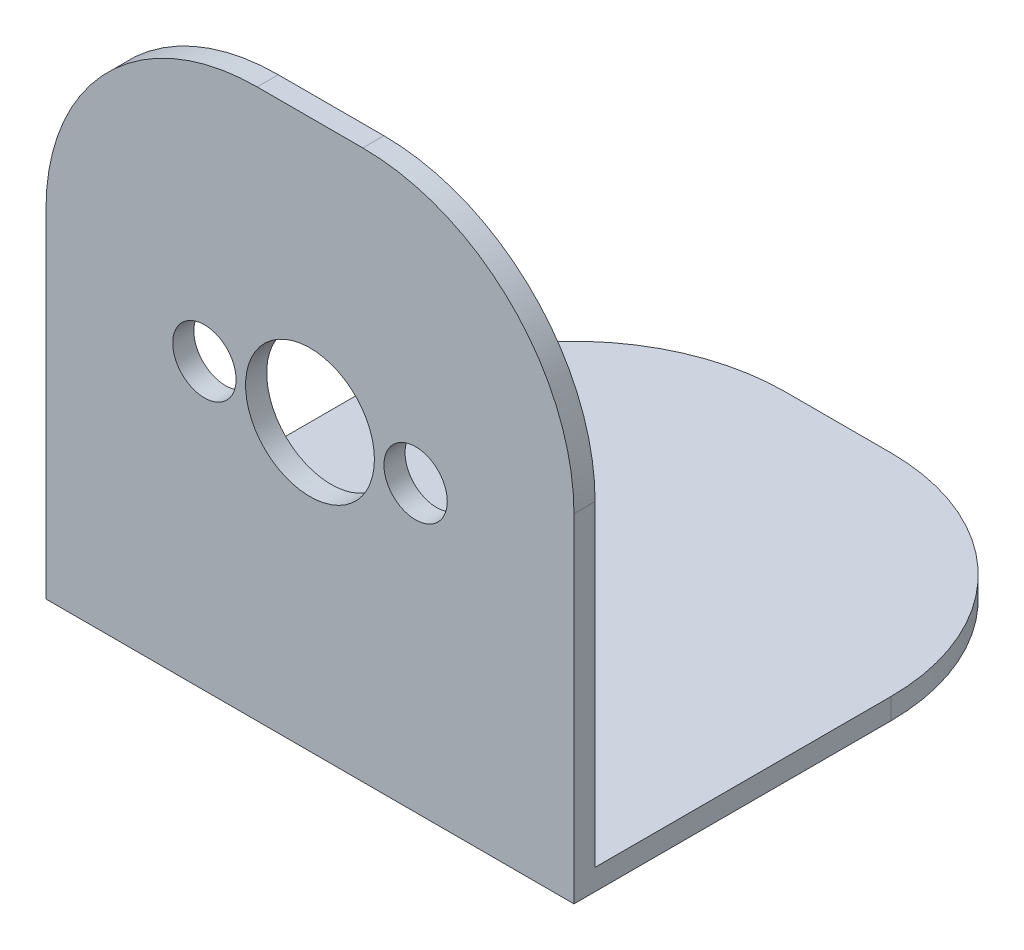
SolidWorks part; units mm, degrees
material "7079 Alloy"
ref_plane "Front" through (0, 0, 0) normal (0, 0, 1) x (1, 0, 0)
ref_plane "Top" through (0, 0, 0) normal (0, 1, 0) x (1, 0, 0)
ref_plane "Right" through (0, 0, 0) normal (1, 0, 0) x (0, 0, -1)
sketch "Sketch1" plane through (0, 0, 0) normal (0, 0, 1) x (1, 0, 0)
  line L1 (0, 0) -> (25, 0)
  line L2 (0, 0) -> (0, 25)
  line L3 (0, 25) -> (25, 25)
  line L4 (25, 0) -> (25, 25)
  circle A1 centre (12.5, 12.5) radius 3.05
  circle A2 centre (17.5, 12.5) radius 1.5
  circle A3 centre (7.5, 12.5) radius 1.5
  dimension "D3" = 10
  dimension "D4" = 6.1
  dimension "D5" = 3
  dimension "D6" = 3
  dimension "D1" = 25
  dimension "D2" = 25
  dimension "D7" = 12.5
extrude "Extrude1" add sketch "Sketch1" along normal blind 1
sketch "Sketch2" plane through (0, 0, 0) normal (0, -1, 0) x (1, 0, 0)
  line L1 (0, 1) -> (25, 1)
  line L2 (0, 1) -> (0, -24)
  line L3 (0, -24) -> (25, -24)
  line L4 (25, 1) -> (25, -24)
  dimension "D1" = 25
  dimension "D2" = 25
extrude "Extrude2" add sketch "Sketch2" along normal blind 1
fillet "Fillet1" radius 10 4 edges at (0, -0.5, -24) (25, -0.5, -24) (0, 25, 0.5) (25, 25, 0.5)
